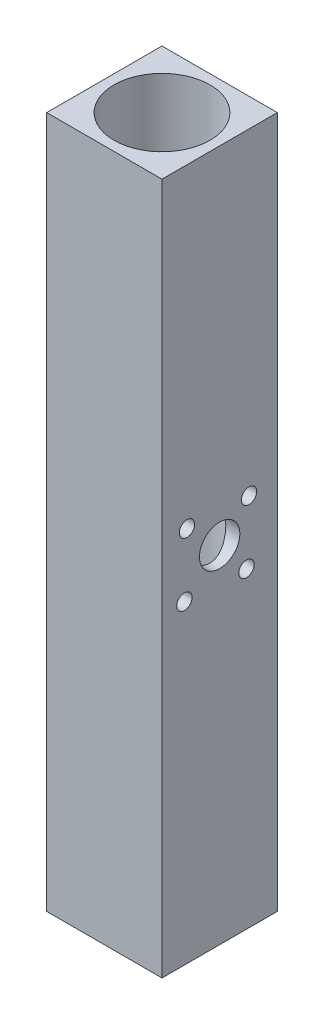
SolidWorks part; units mm, degrees
ref_plane "Front Plane" through (0, 0, 0) normal (0, 0, 1) x (1, 0, 0)
ref_plane "Top Plane" through (0, 0, 0) normal (0, 1, 0) x (1, 0, 0)
ref_plane "Right Plane" through (0, 0, 0) normal (1, 0, 0) x (0, 0, -1)
sketch "Sketch1" plane through (0, 0, 0) normal (0, 1, 0) x (1, 0, 0)
  line L0 (0, 76.2) -> (76.2, 0) construction
  line L1 (0, 0) -> (76.2, 0)
  line L2 (0, 0) -> (0, 76.2)
  line L3 (0, 76.2) -> (76.2, 76.2)
  line L4 (76.2, 0) -> (76.2, 76.2)
  line L5 (76.2, 76.2) -> (0, 0) construction
  circle A0 centre (38.1, 38.1) radius 31.75
  dimension "D3" = 63.5
  dimension "D1" = 76.2
  dimension "D2" = 76.2
extrude "Boss-Extrude1" add sketch "Sketch1" along normal blind 457.2
sketch "Sketch2" plane through (0, 0, 0) normal (-1, 0, 0) x (0, 0, 1)
  line L1 (-38.1, 457.2) -> (-38.1, 0) construction
  line L2 (-76.2, 457.2) -> (0, 457.2) construction
  line L3 (-76.2, 0) -> (0, 0) construction
  circle A0 centre (-38.1, 228.6) radius 13.335
  dimension "D1" = 26.67
extrude "Cut-Extrude1" cut sketch "Sketch2" against normal blind 914.4
sketch "Sketch3" plane through (0, 0, 0) normal (-1, 0, 0) x (0, 0, 1)
  line L0 (-38.1, 241.935) -> (-38.1, 215.265) construction
  line L1 (-65.1359, 239.6273) -> (-49.8959, 254.8673) construction
  circle A0 centre (-38.1, 228.6) radius 13.335 construction
  circle A1 centre (-38.1, 228.6) radius 13.335 construction
  circle A2 centre (-57.5159, 247.2473) radius 5.08
  circle A3 centre (-16.5221, 248.9563) radius 5.08
  circle A4 centre (-14.8131, 207.9624) radius 5.08
  circle A5 centre (-55.8069, 206.2534) radius 5.08
  point P17 (-38.1, 228.6)
  dimension "D1" = 10.16
  dimension "D2" = 10.16
  dimension "D3" = 10.16
  dimension "D4" = 10.16
extrude "Cut-Extrude2" cut sketch "Sketch3" against normal blind 914.4
